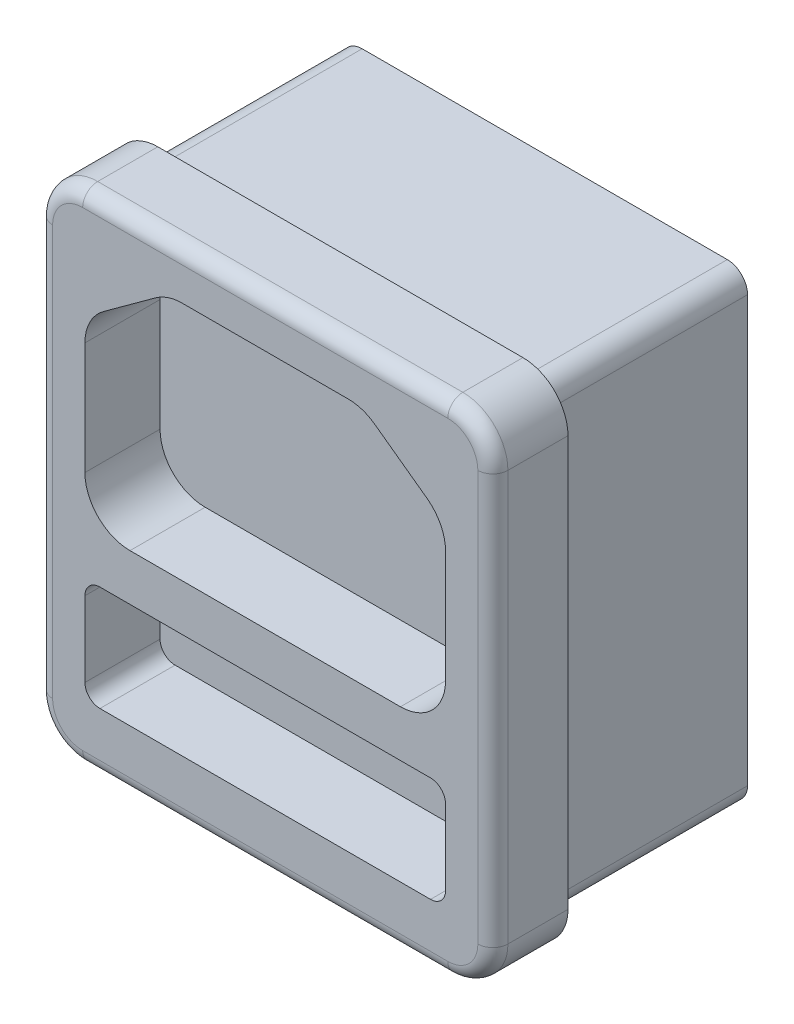
SolidWorks part; units mm, degrees
material "ABS"
ref_plane "Front Plane" through (0, 0, 0) normal (0, 0, 1) x (1, 0, 0)
ref_plane "Top Plane" through (0, 0, 0) normal (0, 1, 0) x (1, 0, 0)
ref_plane "Right Plane" through (0, 0, 0) normal (1, 0, 0) x (0, 0, -1)
sketch "Sketch1" plane through (0, 0, 0) normal (0, 0, 1) x (1, 0, 0)
  line L0 (0, 30.6695) -> (0, -39.7841) construction
  line L1 (-44.0951, 0) -> (41.878, 0) construction
  line L2 (-5.5244, 13.45) -> (5.5244, 13.45)
  line L3 (-12.15, -16.65) -> (12.15, -16.65)
  line L4 (-15.15, -13.65) -> (-15.15, 13.65)
  line L5 (-12.15, 16.65) -> (12.15, 16.65)
  line L6 (15.15, -13.65) -> (15.15, 13.65)
  line L7 (-15.15, -16.65) -> (15.15, 16.65) construction
  line L8 (-15.15, 16.65) -> (15.15, -16.65) construction
  line L9 (-9, -2.55) -> (9, -2.55)
  line L10 (-12, 0.45) -> (-12, 7.9223)
  line L11 (-10.7645, 10.3485) -> (-7.289, 12.8762)
  line L12 (7.289, 12.8762) -> (10.7645, 10.3485)
  line L13 (12, 7.9223) -> (12, 0.45)
  line L14 (-12, -6.65) -> (-12, -11.65)
  line L15 (-11, -12.65) -> (11, -12.65)
  line L16 (12, -11.65) -> (12, -6.65)
  line L17 (11, -5.65) -> (-11, -5.65)
  arc A0 (12.15, 16.65) -> (15.15, 13.65) centre (12.15, 13.65) cw
  arc A1 (12.15, -16.65) -> (15.15, -13.65) centre (12.15, -13.65) ccw
  arc A2 (-12.15, -16.65) -> (-15.15, -13.65) centre (-12.15, -13.65) cw
  arc A3 (-15.15, 13.65) -> (-12.15, 16.65) centre (-12.15, 13.65) cw
  arc A4 (10.7645, 10.3485) -> (12, 7.9223) centre (9, 7.9223) cw
  arc A5 (-12, 7.9223) -> (-10.7645, 10.3485) centre (-9, 7.9223) cw
  arc A6 (5.5244, 13.45) -> (7.289, 12.8762) centre (5.5244, 10.45) cw
  arc A7 (-5.5244, 13.45) -> (-7.289, 12.8762) centre (-5.5244, 10.45) ccw
  arc A8 (9, -2.55) -> (12, 0.45) centre (9, 0.45) ccw
  arc A9 (-9, -2.55) -> (-12, 0.45) centre (-9, 0.45) cw
  arc A10 (11, -12.65) -> (12, -11.65) centre (11, -11.65) ccw
  arc A11 (12, -6.65) -> (11, -5.65) centre (11, -6.65) ccw
  arc A12 (-12, -11.65) -> (-11, -12.65) centre (-11, -11.65) ccw
  arc A13 (-12, -6.65) -> (-11, -5.65) centre (-11, -6.65) cw
  point P5 (0, 0)
  point P26 (0, 13.45)
  point P27 (0, -2.55)
  point P37 (-12, 9.45)
  point P40 (6.5, 13.45)
  point P43 (-6.5, 13.45)
  point P46 (12, -2.55)
  point P49 (-12, -2.55)
  dimension "D3" = 3
  dimension "D9" = 3
  dimension "D10" = 3
  dimension "D11" = 1
  dimension "D1" = 33.3
  dimension "D2" = 30.3
  dimension "D4" = 3.2
  dimension "D5" = 16
  dimension "D6" = 24
  dimension "D7" = 12
  dimension "D8" = 13
  dimension "D12" = 4
  dimension "D13" = 7
extrude "Boss-Extrude1" add sketch "Sketch1" along normal blind 5 contours L5 A0 L6 A1 L3 A2 L4 A3
fillet "Fillet3" radius 1 8 edges at (14.2713, 15.7713, 5) (15.15, 0, 5) (14.2713, -15.7713, 5) (0, -16.65, 5) (-14.2713, -15.7713, 5) (-15.15, 0, 5) (-14.2713, 15.7713, 5) (0, 16.65, 5)
sketch "Sketch3" plane through (0, 0, 0) normal (0, 0, -1) x (-1, 0, 0)
  line L4 (-12.15, 16.65) -> (12.15, 16.65) construction
  line L5 (-15.15, -13.65) -> (-15.15, 13.65) construction
  line L6 (12.15, -16.65) -> (-12.15, -16.65) construction
  line L7 (15.15, 13.65) -> (15.15, -13.65) construction
  line L12 (-13.5, 14.15) -> (-13.5, -14.15)
  line L13 (-12.15, -15.5) -> (12.15, -15.5)
  line L14 (13.5, -14.15) -> (13.5, 14.15)
  line L15 (12.15, 15.5) -> (-12.15, 15.5)
  arc A12 (-12.15, 15.5) -> (-13.5, 14.15) centre (-12.15, 14.15) ccw
  arc A13 (-13.5, -14.15) -> (-12.15, -15.5) centre (-12.15, -14.15) ccw
  arc A14 (12.15, -15.5) -> (13.5, -14.15) centre (12.15, -14.15) ccw
  arc A15 (13.5, 14.15) -> (12.15, 15.5) centre (12.15, 14.15) ccw
  dimension "D1" = 1.15
  dimension "D2" = 1.65
  dimension "D3" = 1.15
  dimension "D4" = 1.65
extrude "Boss-Extrude2" add sketch "Sketch3" along normal blind 13.6
